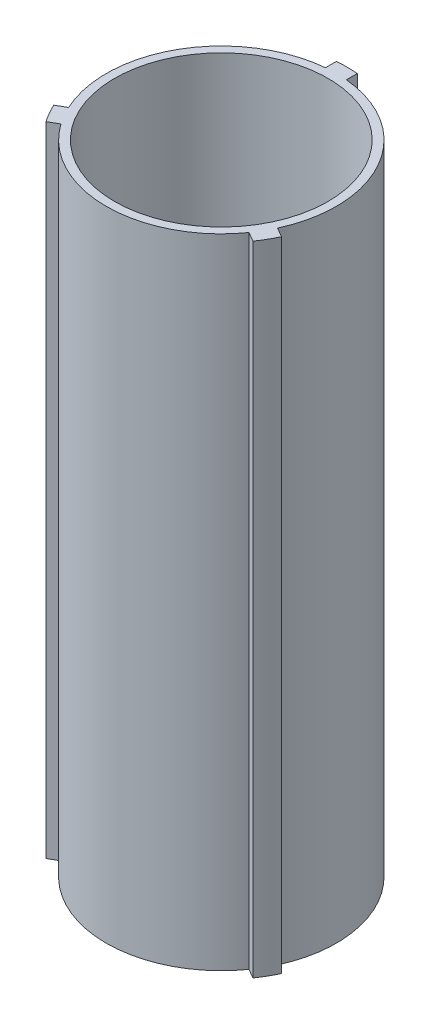
SolidWorks part; units mm, degrees
ref_plane "Front Plane" through (0, 0, 0) normal (0, 0, 1) x (1, 0, 0)
ref_plane "Top Plane" through (0, 0, 0) normal (0, 1, 0) x (1, 0, 0)
ref_plane "Right Plane" through (0, 0, 0) normal (1, 0, 0) x (0, 0, -1)
sketch "Sketch1" plane through (0, 0, 0) normal (0, 1, 0) x (1, 0, 0)
  line L0 (-3.175, 34.7804) -> (-3.175, 38.0949)
  line L1 (3.175, 34.7804) -> (-3.175, 34.7804) construction
  line L2 (3.175, 38.0949) -> (3.175, 34.7804)
  line L3 (31.7082, -14.6406) -> (34.5787, -16.2978)
  line L5 (31.4037, -21.7971) -> (28.5332, -20.1398)
  line L6 (-28.5332, -20.1398) -> (-31.4037, -21.7971)
  line L8 (-34.5787, -16.2978) -> (-31.7082, -14.6406)
  arc A0 (-34.5787, -16.2978) -> (-31.4037, -21.7971) centre (0, 0) ccw
  arc A1 (-28.5332, -20.1398) -> (28.5332, -20.1398) centre (0, 0) ccw
  arc A2 (3.175, 38.0949) -> (-3.175, 38.0949) centre (0, 0) ccw
  arc A3 (31.4037, -21.7971) -> (34.5787, -16.2978) centre (0, 0) ccw
  arc A4 (-3.175, 34.7804) -> (-31.7082, -14.6406) centre (0, 0) ccw
  arc A5 (31.7082, -14.6406) -> (3.175, 34.7804) centre (0, 0) ccw
  circle A6 centre (0, 0) radius 32.385
  point P3 (0, 34.7804)
  point P19 (0, 0)
  dimension "D1" = 76.454
  dimension "D4" = 69.85
  dimension "D5" = 64.77
  dimension "D2" = 6.35
  dimension "D3" = 3
extrude "Boss-Extrude1" add sketch "Sketch1" along normal blind 193.675
